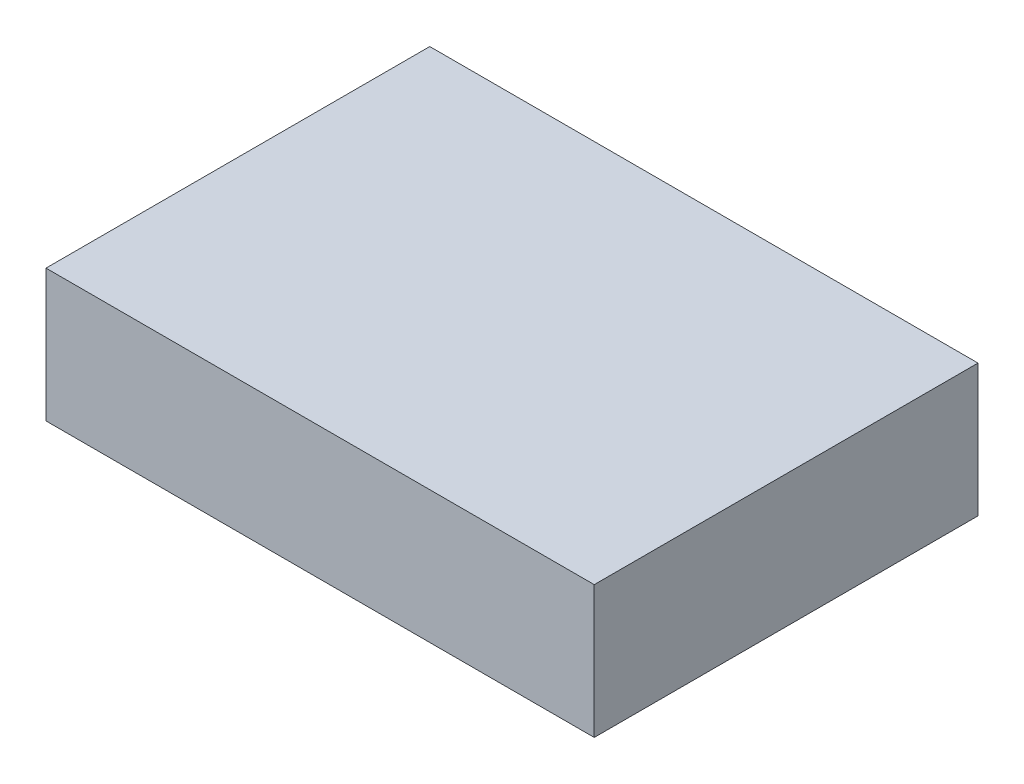
SolidWorks part; units mm, degrees
ref_plane "Front Plane" through (0, 0, 0) normal (0, 0, 1) x (1, 0, 0)
ref_plane "Top Plane" through (0, 0, 0) normal (0, 1, 0) x (1, 0, 0)
ref_plane "Right Plane" through (0, 0, 0) normal (1, 0, 0) x (0, 0, -1)
sketch "Sketch1" plane through (0, 0, 0) normal (0, 0, 1) x (1, 0, 0)
  line L1 (-7, 1.69) -> (7, 1.69)
  line L2 (-7, 1.69) -> (-7, -1.69)
  line L3 (-7, -1.69) -> (7, -1.69)
  line L4 (7, 1.69) -> (7, -1.69)
  line L5 (-7, 1.69) -> (7, -1.69) construction
  line L6 (-7, -1.69) -> (7, 1.69) construction
  point P0 (0, 0)
  dimension "D1" = 14
  dimension "D2" = 3.38
extrude "Boss-Extrude1" add sketch "Sketch1" along normal blind 9.8
sketch "Sketch2" plane through (0, -1.69, 0) normal (0, -1, 0) x (1, 0, 0)
  line L0 (-7, 4.9) -> (7, 4.9) construction
  line L1 (-7, 9.8) -> (-7, 0) construction
  line L2 (7, 9.8) -> (7, 0) construction
  text T0 "  ML2"
extrude "Boss-Extrude2" add sketch "Sketch2" along normal blind 0.0001
